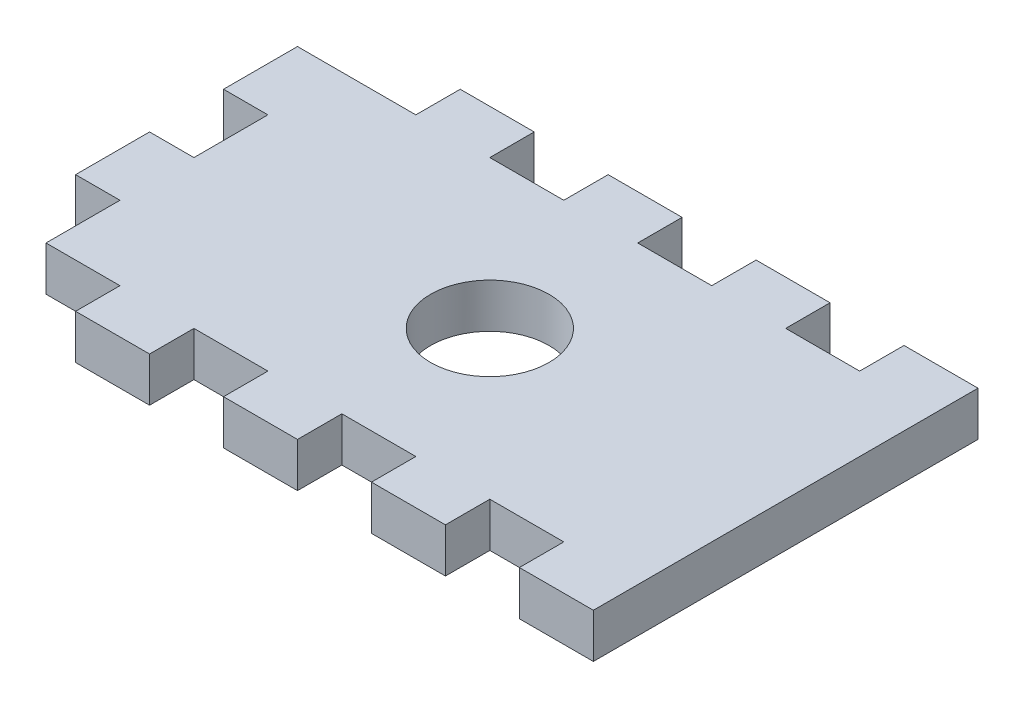
SolidWorks part; units mm, degrees
ref_plane "Front Plane" through (0, 0, 0) normal (0, 0, 1) x (1, 0, 0)
ref_plane "Top Plane" through (0, 0, 0) normal (0, 1, 0) x (1, 0, 0)
ref_plane "Right Plane" through (0, 0, 0) normal (1, 0, 0) x (0, 0, -1)
sketch "Sketch1" plane through (0, 0, 0) normal (0, 1, 0) x (1, 0, 0)
  line L1 (-20, 13) -> (20, 13)
  line L2 (-20, 13) -> (-20, -13)
  line L3 (-20, -13) -> (20, -13)
  line L4 (20, 13) -> (20, -13)
  line L5 (-20, 13) -> (20, -13) construction
  line L6 (-20, -13) -> (20, 13) construction
  point P0 (0, 0)
  dimension "D1" = 40
  dimension "D2" = 26
extrude "Boss-Extrude1" add sketch "Sketch1" along normal mid plane 3
sketch "Sketch2" plane through (0, -1.5, 0) normal (0, -1, 0) x (1, 0, 0)
  circle A0 centre (0, 0) radius 4
  point P2 (0, 0)
  point P3 (0, -5.0471)
  point P4 (0, -7.6882)
  point P7 (0, 0)
  dimension "D1" = 8
extrude "Cut-Extrude1" cut sketch "Sketch2" against normal up to surface (3 mm away) up to face at (0, 1.5, 0)
sketch "Sketch8" plane through (-20, 0, 0) normal (-1, 0, 0) x (0, 0, 1)
  line L0 (-13, -1.5) -> (13, -1.5) construction
  line L1 (-13, 1.5) -> (-10, 1.5)
  line L2 (-13, 1.5) -> (-13, -1.5)
  line L3 (-13, -1.5) -> (-10, -1.5)
  line L4 (-10, 1.5) -> (-10, -1.5)
  line L6 (13, 1.5) -> (10, 1.5)
  line L7 (13, 1.5) -> (13, -1.5)
  line L8 (13, -1.5) -> (10, -1.5)
  line L9 (10, 1.5) -> (10, -1.5)
  line L10 (-10, 1.5) -> (-5, 1.5)
  line L11 (-10, 1.5) -> (-10, -1.5)
  line L12 (-10, -1.5) -> (-5, -1.5)
  line L13 (-5, 1.5) -> (-5, -1.5)
  line L18 (5, 1.5) -> (10, 1.5)
  line L19 (5, 1.5) -> (5, -1.5)
  line L20 (5, -1.5) -> (10, -1.5)
  line L21 (10, 1.5) -> (10, -1.5)
  line L22 (-5, 1.5) -> (0, 1.5)
  line L23 (-5, 1.5) -> (-5, -1.5)
  line L24 (-5, -1.5) -> (0, -1.5)
  line L25 (0, 1.5) -> (0, -1.5)
  line L26 (0, 1.5) -> (5, 1.5)
  line L27 (0, 1.5) -> (0, -1.5)
  line L28 (0, -1.5) -> (5, -1.5)
  line L29 (5, 1.5) -> (5, -1.5)
  line M12 (-13, -1.5) -> (13, -1.5)
  line M14 (13, 1.5) -> (-13, 1.5)
  dimension "D1" = 3
extrude "Boss-Extrude7" add sketch "Sketch8" along normal blind 3 contours L13 L4 M14 M12 | L25 L19 M14 M12
sketch "Sketch9" plane through (0, -1.5, 0) normal (0, -1, 0) x (1, 0, 0)
  line L0 (-23, -10) -> (-20, -10) construction
  line L1 (-20, -13) -> (-15, -13)
  line L2 (-20, -13) -> (-20, -10)
  line L3 (-20, -10) -> (-15, -10)
  line L4 (-15, -13) -> (-15, -10)
  line L5 (0, 0) -> (-5.3473, 0) construction
  line L6 (-15, -13) -> (-10, -13)
  line L7 (-15, -13) -> (-15, -10)
  line L8 (-15, -10) -> (-10, -10)
  line L9 (-10, -13) -> (-10, -10)
  line L10 (-10, -13) -> (-5, -13)
  line L11 (-10, -13) -> (-10, -10)
  line L12 (-10, -10) -> (-5, -10)
  line L13 (-5, -13) -> (-5, -10)
  line L14 (-10, 10) -> (-5, 10)
  line L15 (-5, 13) -> (-5, 10)
  line L16 (-10, 13) -> (-5, 13)
  line L17 (-10, 13) -> (-10, 10)
  line L18 (-15, 10) -> (-10, 10)
  line L19 (-10, 13) -> (-10, 10)
  line L20 (-15, 13) -> (-10, 13)
  line L21 (-15, 13) -> (-15, 10)
  line L22 (-20, 10) -> (-15, 10)
  line L23 (-15, 13) -> (-15, 10)
  line L24 (-20, 13) -> (-15, 13)
  line L25 (-20, 13) -> (-20, 10)
  line L26 (15, 10) -> (20, 10)
  line L27 (-5, -13) -> (0, -13)
  line L28 (-5, -13) -> (-5, -10)
  line L29 (-5, -10) -> (0, -10)
  line L30 (0, -13) -> (0, -10)
  line L31 (0, -13) -> (5, -13)
  line L32 (0, -13) -> (0, -10)
  line L33 (0, -10) -> (5, -10)
  line L34 (5, -13) -> (5, -10)
  line L35 (5, -13) -> (10, -13)
  line L36 (5, -13) -> (5, -10)
  line L37 (5, -10) -> (10, -10)
  line L38 (10, -13) -> (10, -10)
  line L39 (10, -13) -> (15, -13)
  line L40 (10, -13) -> (10, -10)
  line L41 (10, -10) -> (15, -10)
  line L42 (15, -13) -> (15, -10)
  line L43 (15, -13) -> (20, -13)
  line L44 (15, -13) -> (15, -10)
  line L45 (15, -10) -> (20, -10)
  line L46 (20, -13) -> (20, -10)
  line L47 (20, 13) -> (20, 10)
  line L48 (15, 13) -> (20, 13)
  line L49 (15, 13) -> (15, 10)
  line L50 (10, 10) -> (15, 10)
  line L51 (15, 13) -> (15, 10)
  line L52 (10, 13) -> (15, 13)
  line L53 (10, 13) -> (10, 10)
  line L54 (5, 10) -> (10, 10)
  line L55 (10, 13) -> (10, 10)
  line L56 (5, 13) -> (10, 13)
  line L57 (5, 13) -> (5, 10)
  line L58 (0, 10) -> (5, 10)
  line L59 (5, 13) -> (5, 10)
  line L60 (0, 13) -> (5, 13)
  line L61 (0, 13) -> (0, 10)
  line L62 (-5, 10) -> (0, 10)
  line L63 (0, 13) -> (0, 10)
  line L64 (-5, 13) -> (0, 13)
  line L65 (-5, 13) -> (-5, 10)
  line M11 (20, 13) -> (-20, 13)
  line M12 (-20, 13) -> (-20, 5)
  line M20 (-20, -10) -> (-20, -13)
  line M21 (-20, -13) -> (20, -13)
  dimension "D1" = 5
extrude "Cut-Extrude2" cut sketch "Sketch9" against normal up to surface (3 mm away) contours L4 L3 M21 M20 | L13 L12 L9 M21 | L22 L21 M12 M11 | L17 L14 L15 M11 | L61 L58 L57 M11 | L53 L50 L49 M11 | L32 L31 L34 L33 | L40 L39 L42 L41
